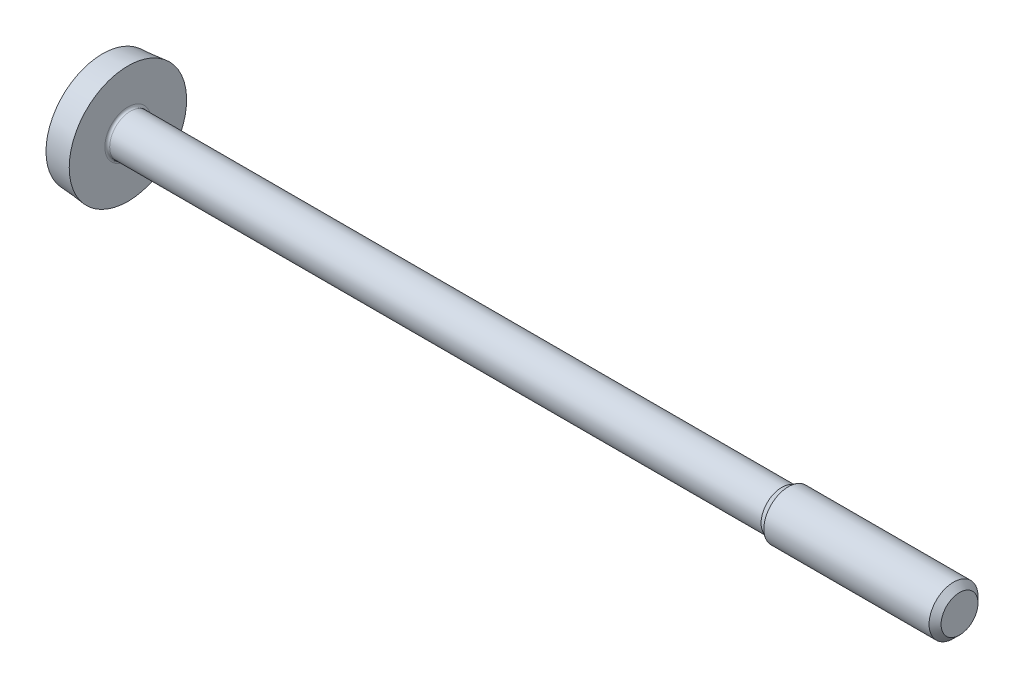
SolidWorks part; units mm, degrees
ref_plane "Front Plane" through (0, 0, 0) normal (0, 0, 1) x (1, 0, 0)
ref_plane "Top Plane" through (0, 0, 0) normal (0, 1, 0) x (1, 0, 0)
ref_plane "Right Plane" through (0, 0, 0) normal (1, 0, 0) x (0, 0, -1)
ref_plane "Plane1" through (0, 0, 0) normal (0, 0, 1) x (1, 0, 0)
sketch "Sketch1" plane through (0, 0, 0) normal (0, 0, 1) x (1, 0, 0)
  line L0 (-1.04, 2.309) -> (0, 2.4)
  line L1 (0, 2.4) -> (0, 0.945)
  line L2 (0.1, 0.845) -> (26.7315, 0.845)
  line L3 (26.7315, 0.845) -> (27, 1)
  line L4 (27, 1) -> (33.7545, 1)
  line L5 (33.7545, 1) -> (34, 0.7545)
  line L6 (34, 0.7545) -> (34, 0)
  line L7 (34, 0) -> (-1.6, 0)
  line L8 (34, 0) -> (-1.6, 0) construction
  arc A0 (-1.6, 0) -> (-1.04, 2.309) centre (3.4403, 0) cw
  arc A1 (0, 0.945) -> (0.1, 0.845) centre (0.1, 0.945) ccw
revolve "Revolve1" add sketch "Sketch1" angle 360 about L8
cosmetic thread "Cosmetic Thread1" parameters "D1"=7, "D2"=1.509
ref_plane "Plane2" through (-1.04, 0, 0) normal (1, 0, 0) x (0, 0, -1)
sketch "Sketch2" plane through (-1.04, 0, 0) normal (1, 0, 0) x (0, 0, -1)
  line L0 (-1, 0.29) -> (-1, -0.29)
  line L1 (-1, -0.29) -> (-0.29, -0.29)
  line L2 (-0.29, -0.29) -> (-0.29, -2.5)
  line L3 (-0.29, -2.5) -> (0.29, -2.5)
  line L4 (0.29, -2.5) -> (0.29, -0.29)
  line L5 (0.29, -0.29) -> (1, -0.29)
  line L6 (1, -0.29) -> (1, 0.29)
  line L7 (1, 0.29) -> (0.29, 0.29)
  line L8 (0.29, 0.29) -> (0.29, 2.5)
  line L9 (0.29, 2.5) -> (-0.29, 2.5)
  line L10 (-0.29, 2.5) -> (-0.29, 0.29)
  line L11 (-0.29, 0.29) -> (-1, 0.29)
extrude "Cut-Extrude1" cut sketch "Sketch2" against normal blind 0.6
